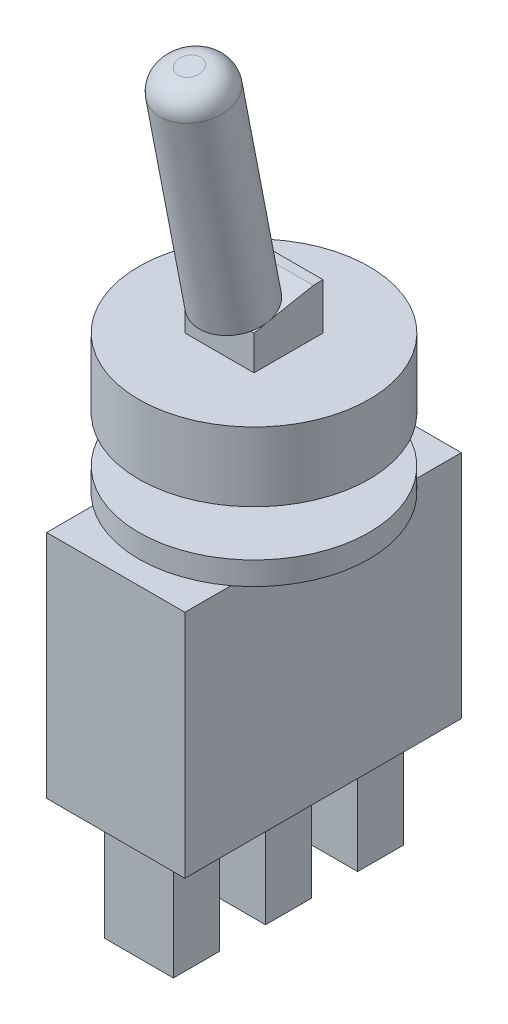
SolidWorks part; units mm, degrees
ref_plane "Plan de face" through (0, 0, 0) normal (0, 0, 1) x (1, 0, 0)
ref_plane "Plan de dessus" through (0, 0, 0) normal (0, 1, 0) x (1, 0, 0)
ref_plane "Plan de droite" through (0, 0, 0) normal (1, 0, 0) x (0, 0, -1)
sketch "Esquisse1" plane through (0, 0, 0) normal (0, 1, 0) x (1, 0, 0)
  circle A0 centre (0, 0) radius 5
  dimension "D1" = 10
extrude "Extrusion1" add sketch "Esquisse1" along normal blind 3
sketch "Esquisse3" plane through (0, 0, 0) normal (0, -1, 0) x (1, 0, 0)
  circle A0 centre (0, 0) radius 2
  dimension "D1" = 4
extrude "Extrusion3" add sketch "Esquisse3" along normal blind 2
sketch "Esquisse4" plane through (0, -2, 0) normal (0, -1, 0) x (1, 0, 0)
  circle A0 centre (0, 0) radius 5
  dimension "D1" = 10
extrude "Extrusion4" add sketch "Esquisse4" along normal blind 1
sketch "Esquisse5" plane through (0, -3, 0) normal (0, -1, 0) x (1, 0, 0)
  line L0 (0, 0) -> (0, 3.7815) construction
  line L1 (3, -6) -> (-3, -6)
  line L2 (3, -6) -> (3, 6)
  line L3 (3, 6) -> (-3, 6)
  line L4 (-3, -6) -> (-3, 6)
  line L5 (-1.6151, 0) -> (1.2087, 0) construction
  dimension "D1" = 6
  dimension "D2" = 3
  dimension "D3" = 6
  dimension "D4" = 12
extrude "Extrusion5" add sketch "Esquisse5" along normal blind 10
sketch "Esquisse6" plane through (0, -13, 0) normal (0, -1, 0) x (1, 0, 0)
  line L0 (0, 8.662) -> (0, -8.4735) construction
  line L1 (-1.5, 3) -> (1.5, 3)
  line L2 (-1.5, 3) -> (-1.5, 5)
  line L3 (-1.5, 5) -> (1.5, 5)
  line L4 (1.5, 3) -> (1.5, 5)
  line L5 (-1.5, -1) -> (1.5, -1)
  line L6 (-1.5, -1) -> (-1.5, 1)
  line L7 (-1.5, 1) -> (1.5, 1)
  line L8 (1.5, -1) -> (1.5, 1)
  line L9 (-1.5, -5) -> (1.5, -5)
  line L10 (-1.5, -5) -> (-1.5, -3)
  line L11 (-1.5, -3) -> (1.5, -3)
  line L12 (1.5, -5) -> (1.5, -3)
  line L13 (-5.4044, 0) -> (7.318, 0) construction
  dimension "D1" = 3
  dimension "D2" = 2
  dimension "D3" = 2
  dimension "D4" = 2
  dimension "D5" = 1
  dimension "D6" = 1.5
  dimension "D7" = 1.5
  dimension "D8" = 1.5
extrude "Extrusion6" add sketch "Esquisse6" along normal blind 5
sketch "Esquisse8" plane through (0, 3, 0) normal (0, 1, 0) x (-1, 0, 0)
  line L1 (1.5, -1.5) -> (-1.5, -1.5)
  line L2 (1.5, -1.5) -> (1.5, 1.5)
  line L3 (1.5, 1.5) -> (-1.5, 1.5)
  line L4 (-1.5, -1.5) -> (-1.5, 1.5)
  circle A0 centre (0, 0) radius 5 construction
  dimension "D1" = 3
  dimension "D2" = 3
  dimension "D3" = 1.5
  dimension "D4" = 1.5
extrude "Extrusion8" add sketch "Esquisse8" along normal blind 2
chamfer "Chanfrein1" distance 0.5 angle 79 1 edges at (0, 5, 1.5)
sketch "Esquisse9" plane through (0, 4.6171, 0.8975) normal (0, 0.9816, 0.1908) x (-1, 0, 0)
  circle A0 centre (0, 0) radius 1.5
  dimension "D1" = 3
extrude "Extrusion9" add sketch "Esquisse9" along normal blind 10
fillet "Congé1" radius 1 1 edges at (0, 14.1472, 4.278)
